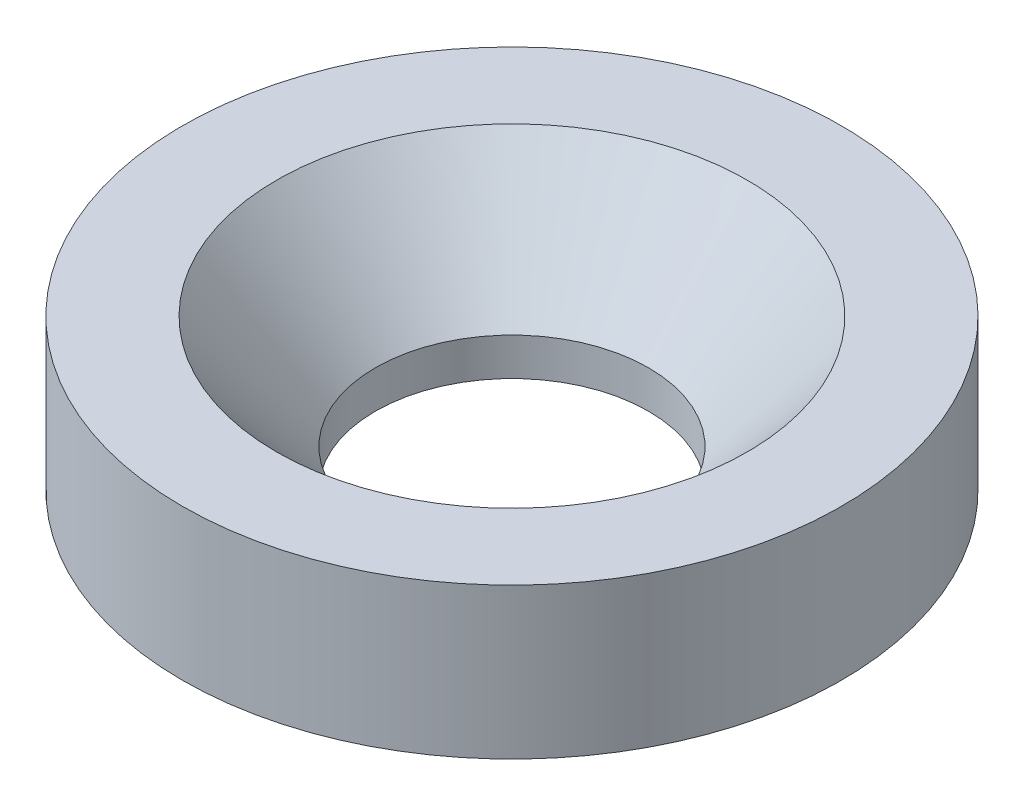
SolidWorks part; units mm, degrees
ref_plane "Front Plane" through (0, 0, 0) normal (0, 0, 1) x (1, 0, 0)
ref_plane "Top Plane" through (0, 0, 0) normal (0, 1, 0) x (1, 0, 0)
ref_plane "Right Plane" through (0, 0, 0) normal (1, 0, 0) x (0, 0, -1)
sketch "Sketch1" plane through (0, 0, 0) normal (0, 0, 1) x (1, 0, 0)
  line L0 (0, 54.443) -> (0, -78.5633) construction
  line L1 (7.25, -65.1248) -> (17.5, -65.1248)
  line L2 (17.5, -65.1248) -> (17.5, -57.1248)
  line L3 (7.25, -65.1248) -> (7.25, -63.1248)
  line L4 (7.25, -63.1248) -> (12.5, -57.1248)
  line L5 (12.5, -57.1248) -> (17.5, -57.1248)
  dimension "D1" = 7.25
  dimension "D2" = 8
  dimension "D3" = 17.5
  dimension "D4" = 12.5
  dimension "D5" = 2
  dimension "D6" = 7.25
  dimension "D7" = 41.186
  dimension "D8" = 12.5
revolve "Revolve1" add sketch "Sketch1" angle 360 about L0
